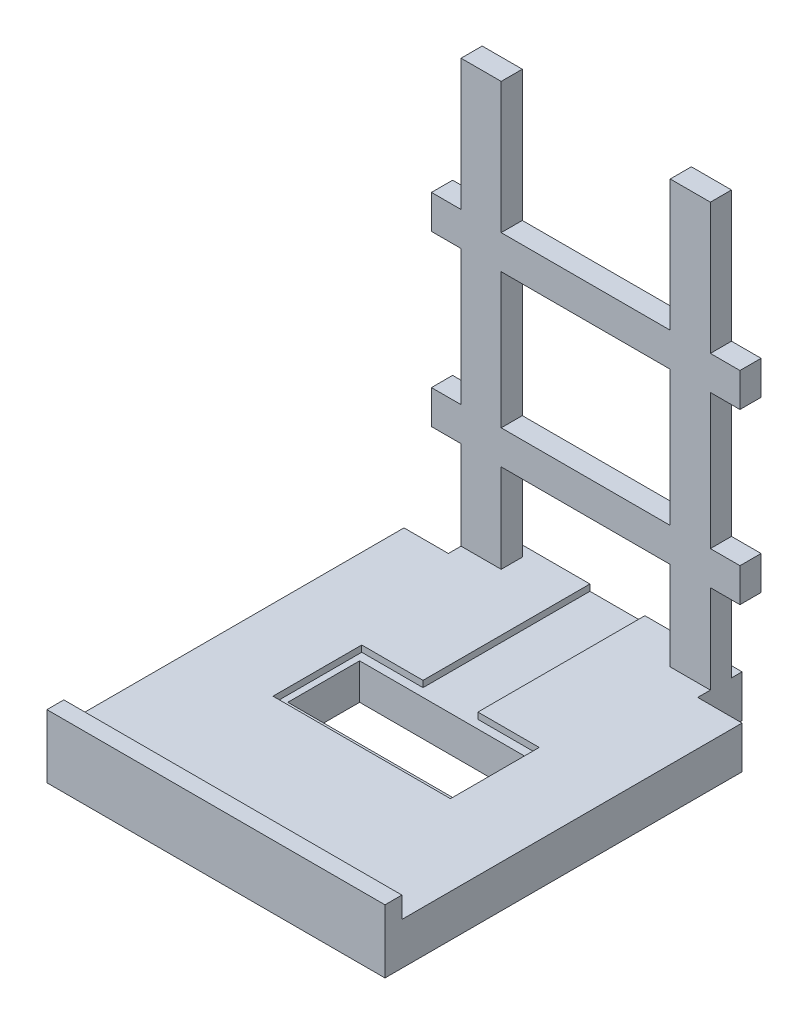
SolidWorks part; units mm, degrees
ref_plane "Front Plane" through (0, 0, 0) normal (0, 0, 1) x (1, 0, 0)
ref_plane "Top Plane" through (0, 0, 0) normal (0, 1, 0) x (1, 0, 0)
ref_plane "Right Plane" through (0, 0, 0) normal (1, 0, 0) x (0, 0, -1)
sketch "Sketch1" plane through (0, 0, 0) normal (0, 1, 0) x (1, 0, 0)
  line L1 (-40, -47.5) -> (40, -47.5)
  line L2 (-40, -47.5) -> (-40, 47.5)
  line L3 (-40, 47.5) -> (40, 47.5)
  line L4 (40, -47.5) -> (40, 47.5)
  line L5 (-40, -47.5) -> (40, 47.5) construction
  line L6 (-40, 47.5) -> (40, -47.5) construction
  point P0 (0, 0)
  dimension "D1" = 95
  dimension "D2" = 80
extrude "Boss-Extrude1" add sketch "Sketch1" along normal blind 10
sketch "Sketch2" plane through (0, 10, 0) normal (0, 1, 0) x (1, 0, 0)
  line L0 (0, 47.5) -> (0, -47.5) construction
  line L1 (-40, 47.5) -> (-30, 47.5)
  line L2 (-40, 47.5) -> (-40, 37.5)
  line L3 (-40, 37.5) -> (-30, 37.5)
  line L4 (-30, 47.5) -> (-30, 37.5)
  line L5 (40, 47.5) -> (-40, 47.5) construction
  line L6 (-40, -47.5) -> (40, -47.5) construction
  line L7 (40, 37.5) -> (30, 37.5)
  line L8 (30, 47.5) -> (30, 37.5)
  line L9 (40, 47.5) -> (30, 47.5)
  line L10 (40, 47.5) -> (40, 37.5)
  dimension "D1" = 10
  dimension "D2" = 10
extrude "Cut-Extrude1" cut sketch "Sketch2" against normal blind 10
sketch "Sketch3" plane through (0, 10, 0) normal (0, 1, 0) x (1, 0, 0)
  line L0 (40, -47.5) -> (40, 37.5) construction
  line L1 (-40, -47.5) -> (40, -47.5)
  line L2 (-40, -47.5) -> (-40, -42.5)
  line L3 (-40, -42.5) -> (40, -42.5)
  line L4 (40, -47.5) -> (40, -42.5)
  dimension "D1" = 5
extrude "Boss-Extrude2" add sketch "Sketch3" along normal blind 5
sketch "Sketch4" plane through (0, 10, 0) normal (0, 1, 0) x (1, 0, 0)
  line L0 (-40, 37.5) -> (40, -42.5) construction
  line L1 (40, 37.5) -> (-40, 37.5) construction
  line L2 (40, 37.5) -> (40, -42.5) construction
  line L3 (40, -42.5) -> (-40, -42.5) construction
  line L4 (-40, 37.5) -> (-40, -42.5) construction
  line L5 (40, 37.5) -> (-40, -42.5) construction
  line L6 (0, -2.5) -> (0, 47.5) construction
  line L7 (-21, -13) -> (21, -13)
  line L8 (-21, -13) -> (-21, 8)
  line L9 (-21, 8) -> (-6.5, 8)
  line L10 (21, -13) -> (21, 8)
  line L11 (-21, -13) -> (21, 8) construction
  line L12 (-21, 8) -> (21, -13) construction
  line L13 (30, 47.5) -> (-30, 47.5) construction
  line L14 (-6.5, 8) -> (-6.5, 47.5)
  line L19 (-6.3944, -2.0938) -> (6.5, 47.5) construction
  line L20 (-6.5, 47.5) -> (6.3567, -1.9487) construction
  line L21 (6.4914, 8) -> (21, 8)
  line L22 (6.4914, 8) -> (6.5, 47.5)
  line L23 (-6.5, 47.5) -> (6.5, 47.5)
  point P4 (0, -2.5)
  point P15 (0, 22.5)
  point P21 (0, 47.5)
  dimension "D1" = 42
  dimension "D2" = 21
  dimension "D3" = 13
extrude "Cut-Extrude2" cut sketch "Sketch4" against normal blind 1.5
sketch "Sketch5" plane through (0, 8.5, 0) normal (0, 1, 0) x (1, 0, 0)
  line L0 (-21, -13) -> (21, 8) construction
  line L1 (-19.5, 6) -> (19.5, 6)
  line L2 (-19.5, 6) -> (-19.5, -11)
  line L3 (-19.5, -11) -> (19.5, -11)
  line L4 (19.5, 6) -> (19.5, -11)
  line L5 (-19.5, 6) -> (19.5, -11) construction
  line L6 (-19.5, -11) -> (19.5, 6) construction
  point P0 (0, -2.5)
  dimension "D1" = 17
  dimension "D2" = 39
extrude "Cut-Extrude3" cut sketch "Sketch5" against normal blind 8.5
sketch "Sketch6" plane through (0, 10, 0) normal (0, 1, 0) x (1, 0, 0)
  line L0 (-30, 37.5) -> (30, 47.5) construction
  line L1 (-30, 47.5) -> (30, 37.5) construction
  line L2 (30, 47.5) -> (30, 37.5) construction
  line L3 (-29.5, 40) -> (-20, 40)
  line L5 (-29.5, 45) -> (-20, 45)
  line L7 (-30, 40) -> (30, 45) construction
  line L8 (-30, 45) -> (30, 40) construction
  line L9 (-30, 47.5) -> (-20, 47.5) construction
  line L10 (-6.5, 47.5) -> (-30, 47.5) construction
  line L11 (-20, 45) -> (-20, 40)
  line L12 (0, 37.5) -> (0, 47.5) construction
  line L13 (40, 37.5) -> (-40, 37.5) construction
  line L14 (-6.5, 47.5) -> (6.5, 47.5) construction
  line L15 (20, 45) -> (20, 40)
  line L16 (-29.5, 40) -> (-29.5, 45)
  line L17 (20, 45) -> (29.5, 45)
  line L18 (29.5, 40) -> (29.5, 45)
  line L19 (20, 40) -> (29.5, 40)
  line L20 (-40, 37.5) -> (-40, -42.5) construction
  line L21 (-40, 37.5) -> (-30, 37.5) construction
  line L22 (-30, 37.5) -> (-30, 47.5) construction
  point P8 (0, 42.5)
  dimension "D1" = 5
  dimension "D2" = 10
  dimension "D3" = 2.5
  dimension "D4" = 2.5
  dimension "D5" = 0.5
  dimension "D6" = 2.5
  dimension "D7" = 2.5
extrude "Boss-Extrude3" add sketch "Sketch6" along normal blind 100
ref_plane "Plane1" through (0, 0, -40) normal (0, 0, 1) x (1, 0, 0)
sketch "Sketch7" plane through (0, 0, -40) normal (0, 0, 1) x (1, 0, 0)
  line L0 (0, 15) -> (0, 35) construction
  line L1 (-40, 15) -> (40, 15) construction
  line L2 (0, 35) -> (0, 75) construction
  line L4 (-36.5, 31) -> (36.5, 31)
  line L5 (-36.5, 31) -> (-36.5, 39)
  line L6 (-36.5, 39) -> (36.5, 39)
  line L7 (36.5, 31) -> (36.5, 39)
  line L8 (-36.5, 31) -> (36.5, 39) construction
  line L9 (-36.5, 39) -> (36.5, 31) construction
  line L10 (-36.5, 71) -> (36.5, 71)
  line L11 (-36.5, 71) -> (-36.5, 79)
  line L12 (-36.5, 79) -> (36.5, 79)
  line L13 (36.5, 71) -> (36.5, 79)
  line L14 (-36.5, 71) -> (36.5, 79) construction
  line L15 (-36.5, 79) -> (36.5, 71) construction
  dimension "D1" = 20
  dimension "D2" = 40
  dimension "D3" = 73
  dimension "D4" = 73
  dimension "D5" = 8
  dimension "D6" = 8
extrude "Boss-Extrude4" add sketch "Sketch7" against normal blind 5
sketch "Sketch8" plane through (0, 15, 0) normal (0, 1, 0) x (1, 0, 0)
  line L0 (40, -47.5) -> (40, -42.5) construction
  line L1 (-40, -42.5) -> (40, -42.5)
  line L2 (-40, -42.5) -> (-40, -43.5)
  line L3 (-40, -43.5) -> (40, -43.5)
  line L4 (40, -42.5) -> (40, -43.5)
  dimension "D1" = 1
extrude "Cut-Extrude4" cut sketch "Sketch8" against normal blind 5
sketch "Sketch9" plane through (0, 10, 0) normal (0, 1, 0) x (1, 0, 0)
  line L0 (30, 47.5) -> (29.5, 47.5)
  line L1 (30, 47.5) -> (6.5, 47.5) construction
  line L2 (29.5, 47.5) -> (29.5, 37)
  line L3 (29.5, 37) -> (40, 37)
  line L4 (40, 37.5) -> (40, -42.5) construction
  line L5 (40, 37) -> (40, 37.5)
  line L6 (40, 37.5) -> (30, 37.5)
  line L7 (30, 37.5) -> (30, 47.5)
  line L8 (0, 47.5) -> (0, -2.5) construction
  line L9 (-40, 37.5) -> (40, -42.5) construction
  line L10 (-40, 37.5) -> (-30, 37.5)
  line L11 (-40, 37) -> (-40, 37.5)
  line L12 (-29.5, 37) -> (-40, 37)
  line L13 (-29.5, 47.5) -> (-29.5, 37)
  line L14 (-30, 47.5) -> (-29.5, 47.5)
  line L15 (-30, 37.5) -> (-30, 47.5)
  dimension "D1" = 0.5
  dimension "D2" = 0.5
extrude "Cut-Extrude5" cut sketch "Sketch9" against normal blind 10
